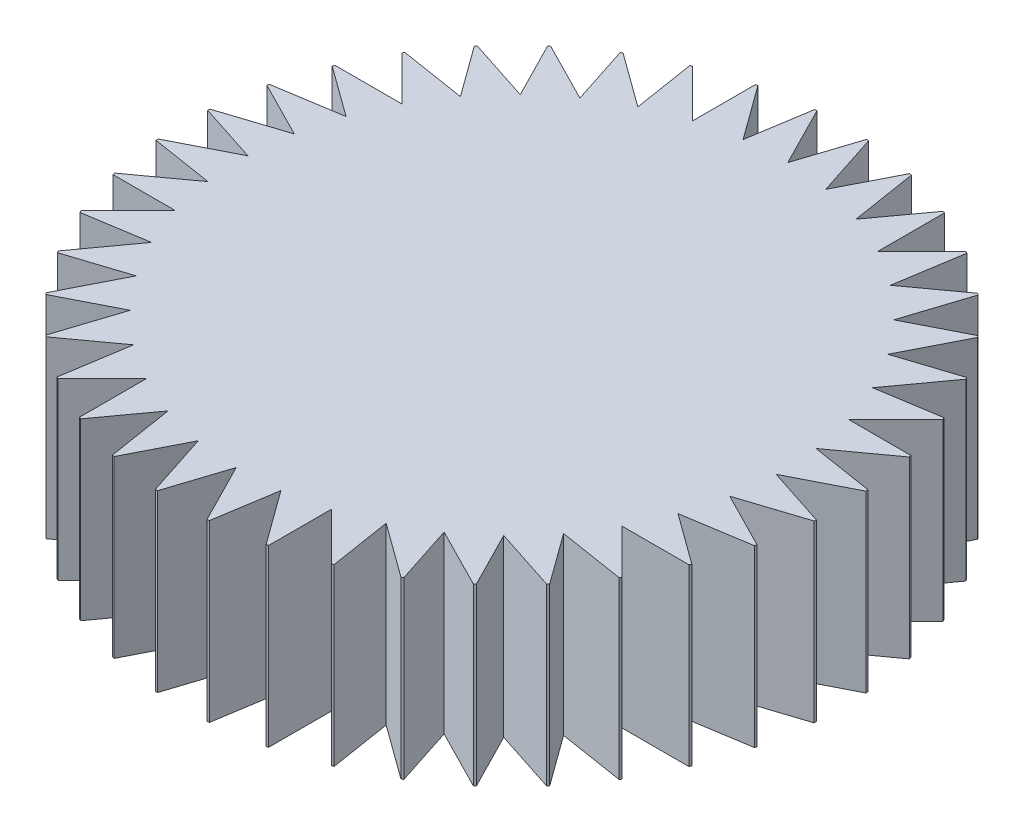
SolidWorks part; units mm, degrees
ref_plane "Ön Düzlem" through (0, 0, 0) normal (0, 0, 1) x (1, 0, 0)
ref_plane "Üst Düzlem" through (0, 0, 0) normal (0, 1, 0) x (1, 0, 0)
ref_plane "Sağ Düzlem" through (0, 0, 0) normal (1, 0, 0) x (0, 0, -1)
sketch "Çizim1" plane through (0, 0, 0) normal (0, 1, 0) x (1, 0, 0)
  line L0 (-2.1468, 5.2472) -> (-1.336, 4.4364)
  line L1 (-1.336, 4.4364) -> (-1.336, 5.5098)
  line L2 (-1.2996, 5.5185) -> (-0.6256, 4.5908)
  line L3 (-0.6256, 4.5908) -> (-0.4576, 5.6509)
  line L4 (-0.4203, 5.6538) -> (0.1003, 4.6321)
  line L5 (0.1003, 4.6321) -> (0.432, 5.653)
  line L6 (0.4693, 5.65) -> (0.8237, 4.5594)
  line L7 (0.8237, 4.5594) -> (1.311, 5.5158)
  line L8 (1.3474, 5.507) -> (1.5268, 4.3744)
  line L9 (1.5268, 4.3744) -> (2.1577, 5.2428)
  line L10 (2.1923, 5.2284) -> (2.1923, 4.0817)
  line L11 (2.1923, 4.0817) -> (2.9513, 4.8407)
  line L12 (2.9832, 4.8211) -> (2.8038, 3.6885)
  line L13 (2.8038, 3.6885) -> (3.6722, 4.3194)
  line L14 (3.7007, 4.2951) -> (3.3463, 3.2045)
  line L15 (3.3463, 3.2045) -> (4.3027, 3.6918)
  line L16 (4.327, 3.6633) -> (3.8064, 2.6415)
  line L17 (3.8064, 2.6415) -> (4.8273, 2.9732)
  line L18 (4.8468, 2.9413) -> (4.1728, 2.0136)
  line L19 (4.1728, 2.0136) -> (5.2329, 2.1815)
  line L20 (5.2472, 2.1468) -> (4.4364, 1.336)
  line L21 (4.4364, 1.336) -> (5.5098, 1.336)
  line L22 (5.5185, 1.2996) -> (4.5908, 0.6256)
  line L23 (4.5908, 0.6256) -> (5.6509, 0.4576)
  line L24 (5.6538, 0.4203) -> (4.6321, -0.1003)
  line L25 (4.6321, -0.1003) -> (5.653, -0.432)
  line L26 (5.65, -0.4693) -> (4.5594, -0.8237)
  line L27 (4.5594, -0.8237) -> (5.5158, -1.311)
  line L28 (5.507, -1.3474) -> (4.3744, -1.5268)
  line L29 (4.3744, -1.5268) -> (5.2428, -2.1577)
  line L30 (5.2284, -2.1923) -> (4.0817, -2.1923)
  line L31 (4.0817, -2.1923) -> (4.8407, -2.9513)
  line L32 (4.8211, -2.9832) -> (3.6885, -2.8038)
  line L33 (3.6885, -2.8038) -> (4.3194, -3.6722)
  line L34 (4.2951, -3.7007) -> (3.2045, -3.3463)
  line L35 (3.2045, -3.3463) -> (3.6918, -4.3027)
  line L36 (3.6633, -4.327) -> (2.6415, -3.8064)
  line L37 (2.6415, -3.8064) -> (2.9732, -4.8273)
  line L38 (2.9413, -4.8468) -> (2.0136, -4.1728)
  line L39 (2.0136, -4.1728) -> (2.1815, -5.2329)
  line L40 (2.1468, -5.2472) -> (1.336, -4.4364)
  line L41 (1.336, -4.4364) -> (1.336, -5.5098)
  line L42 (1.2996, -5.5185) -> (0.6256, -4.5908)
  line L43 (0.6256, -4.5908) -> (0.4576, -5.6509)
  line L44 (0.4203, -5.6538) -> (-0.1003, -4.6321)
  line L45 (-0.1003, -4.6321) -> (-0.432, -5.653)
  line L46 (-0.4693, -5.65) -> (-0.8237, -4.5594)
  line L47 (-0.8237, -4.5594) -> (-1.311, -5.5158)
  line L48 (-1.3474, -5.507) -> (-1.5268, -4.3744)
  line L49 (-1.5268, -4.3744) -> (-2.1577, -5.2428)
  line L50 (-2.1923, -5.2284) -> (-2.1923, -4.0817)
  line L51 (-2.1923, -4.0817) -> (-2.9513, -4.8407)
  line L52 (-2.9832, -4.8211) -> (-2.8038, -3.6885)
  line L53 (-2.8038, -3.6885) -> (-3.6722, -4.3194)
  line L54 (-3.7007, -4.2951) -> (-3.3463, -3.2045)
  line L55 (-3.3463, -3.2045) -> (-4.3027, -3.6918)
  line L56 (-4.327, -3.6633) -> (-3.8064, -2.6415)
  line L57 (-3.8064, -2.6415) -> (-4.8273, -2.9732)
  line L58 (-4.8468, -2.9413) -> (-4.1728, -2.0136)
  line L59 (-4.1728, -2.0136) -> (-5.2329, -2.1815)
  line L60 (-5.2472, -2.1468) -> (-4.4364, -1.336)
  line L61 (-4.4364, -1.336) -> (-5.5098, -1.336)
  line L62 (-5.5185, -1.2996) -> (-4.5908, -0.6256)
  line L63 (-4.5908, -0.6256) -> (-5.6509, -0.4576)
  line L64 (-5.6538, -0.4203) -> (-4.6321, 0.1003)
  line L65 (-4.6321, 0.1003) -> (-5.653, 0.432)
  line L66 (-5.65, 0.4693) -> (-4.5594, 0.8237)
  line L67 (-4.5594, 0.8237) -> (-5.5158, 1.311)
  line L68 (-5.507, 1.3474) -> (-4.3744, 1.5268)
  line L69 (-4.3744, 1.5268) -> (-5.2428, 2.1577)
  line L70 (-5.2284, 2.1923) -> (-4.0817, 2.1923)
  line L71 (-4.0817, 2.1923) -> (-4.8407, 2.9513)
  line L72 (-4.8211, 2.9832) -> (-3.6885, 2.8038)
  line L73 (-3.6885, 2.8038) -> (-4.3194, 3.6722)
  line L74 (-4.2951, 3.7007) -> (-3.2045, 3.3463)
  line L75 (-3.2045, 3.3463) -> (-3.6918, 4.3027)
  line L76 (-3.6633, 4.327) -> (-2.6415, 3.8064)
  line L77 (-2.6415, 3.8064) -> (-2.9732, 4.8273)
  line L78 (-2.9413, 4.8468) -> (-2.0136, 4.1728)
  line L79 (-2.0136, 4.1728) -> (-2.1815, 5.2329)
  circle A0 centre (0, 0) radius 5.6694
  point P125 (0, 0)
  dimension "D1" = 40
extrude "Yükseklik-Ekstrüzyon1" add sketch "Çizim1" along normal blind 3 contours L44 A0 L43 L42 L41 L40 L39 L38 L37 L36 L35 L34 L33 L32 L31 L30 L29 L28 L27 L26 L25 L24 L23 L22 L21 L20 L19 L18 L17 L16 L15 L14 L13 L12 L11
